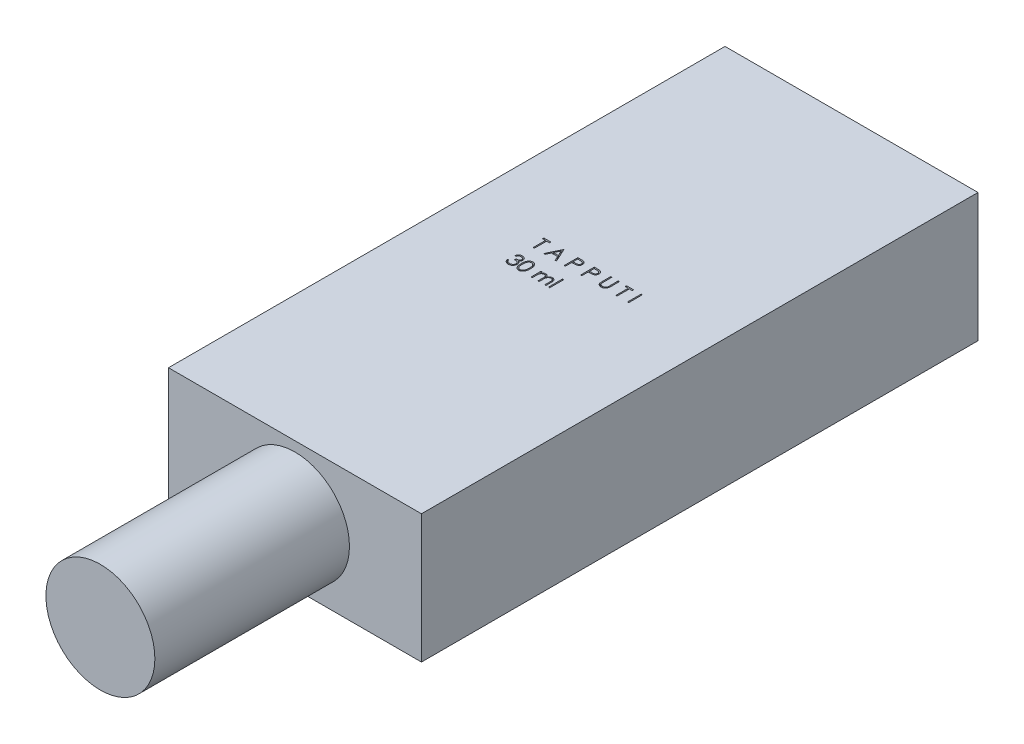
SolidWorks part; units mm, degrees
ref_plane "Front Plane" through (0, 0, 0) normal (0, 0, 1) x (1, 0, 0)
ref_plane "Top Plane" through (0, 0, 0) normal (0, 1, 0) x (1, 0, 0)
ref_plane "Right Plane" through (0, 0, 0) normal (1, 0, 0) x (0, 0, -1)
sketch "Sketch1" plane through (0, 0, 0) normal (0, 1, 0) x (1, 0, 0)
  line L1 (-32.5, 71.5) -> (32.5, 71.5)
  line L2 (-32.5, 71.5) -> (-32.5, -71.5)
  line L3 (-32.5, -71.5) -> (32.5, -71.5)
  line L4 (32.5, 71.5) -> (32.5, -71.5)
  line L5 (-32.5, 71.5) -> (32.5, -71.5) construction
  line L6 (-32.5, -71.5) -> (32.5, 71.5) construction
  point P0 (0, 0)
  dimension "D1" = 65
  dimension "D2" = 143
extrude "Boss-Extrude1" add sketch "Sketch1" against normal blind 33
sketch "Sketch2" plane through (0, 0, 0) normal (0, 1, 0) x (1, 0, 0)
  text T0 "T A P P U T I\r\n30 ml"
extrude "Cut-Extrude1" cut sketch "Sketch2" against normal blind 10
sketch "Sketch4" plane through (0, 0, 71.5) normal (0, 0, 1) x (1, 0, 0)
  line L0 (-32.5, -33) -> (-32.5, 0) construction
  circle A0 centre (0, -16.5) radius 14
  point P2 (0, 0)
  point P6 (-32.5, -16.5)
  dimension "D1" = 28
extrude "Boss-Extrude2" add sketch "Sketch4" along normal blind 50
